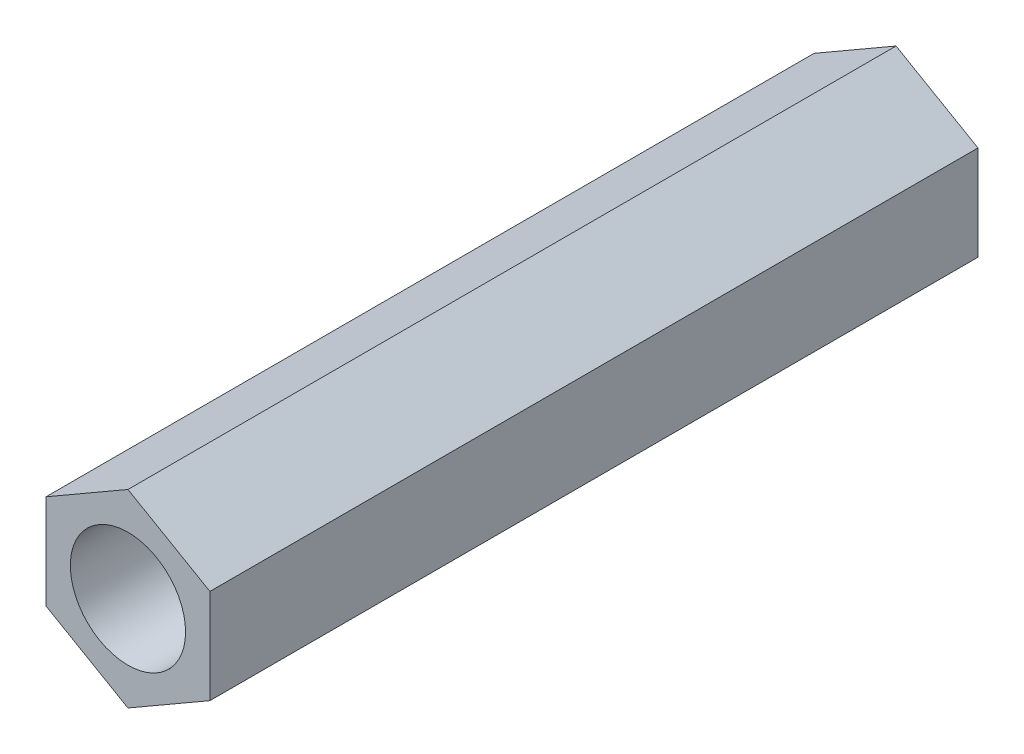
SolidWorks part; units mm, degrees
ref_plane "前视基准面" through (0, 0, 0) normal (0, 0, 1) x (1, 0, 0)
ref_plane "上视基准面" through (0, 0, 0) normal (0, 1, 0) x (1, 0, 0)
ref_plane "右视基准面" through (0, 0, 0) normal (1, 0, 0) x (0, 0, -1)
sketch "草图1" plane through (0, 0, 0) normal (0, 0, 1) x (1, 0, 0)
  line L1 (0, 2.4639) -> (-2.1338, 1.232)
  line L2 (-2.1338, 1.232) -> (-2.1338, -1.232)
  line L3 (-2.1338, -1.232) -> (0, -2.4639)
  line L4 (0, -2.4639) -> (2.1338, -1.232)
  line L5 (2.1338, -1.232) -> (2.1338, 1.232)
  line L6 (2.1338, 1.232) -> (0, 2.4639)
  circle A0 centre (0, 0) radius 1.5
  circle A1 centre (0, 0) radius 2.1338 construction
extrude "凸台-拉伸1" add sketch "草图1" along normal blind 20
